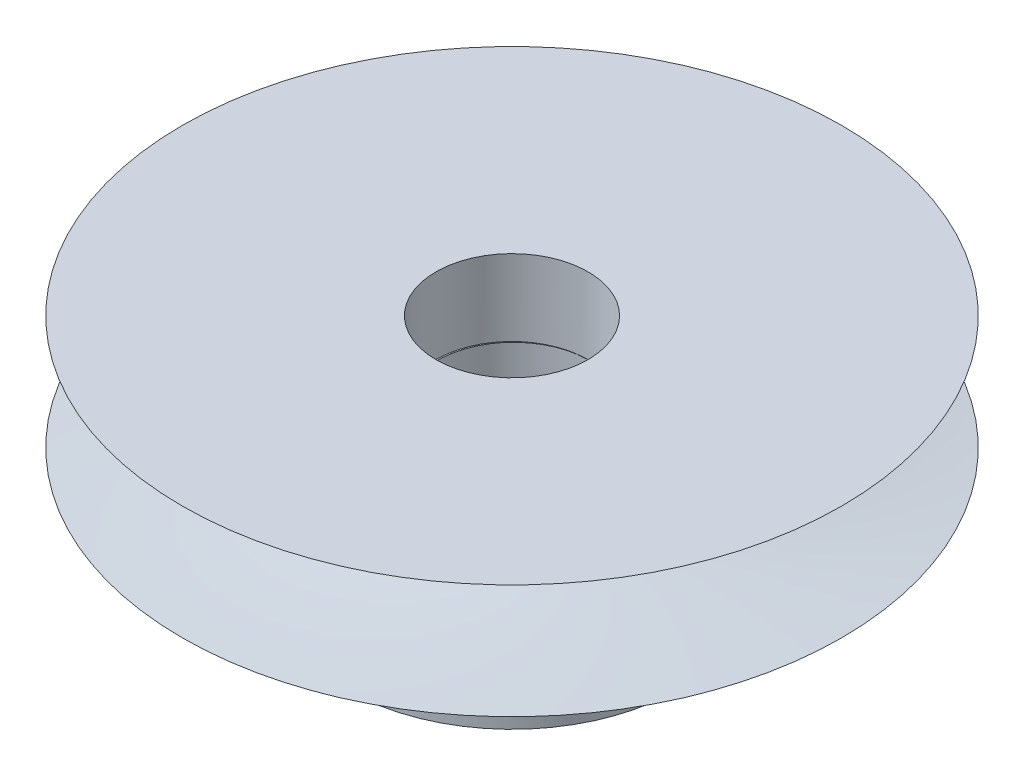
SolidWorks part; units mm, degrees
ref_plane "Front Plane" through (0, 0, 0) normal (0, 0, 1) x (1, 0, 0)
ref_plane "Top Plane" through (0, 0, 0) normal (0, 1, 0) x (1, 0, 0)
ref_plane "Right Plane" through (0, 0, 0) normal (1, 0, 0) x (0, 0, -1)
sketch "Sketch9" plane through (0, 0, 0) normal (0, 0, 1) x (1, 0, 0)
  line L0 (-4.7031, 1.5646) -> (8.2969, -1.4354) construction
  line L1 (-4.7031, -2.9354) -> (8.2969, -2.9354)
  line L3 (-4.7031, 1.5646) -> (8.2969, 1.5646)
  line L4 (8.2969, -2.9354) -> (8.2969, 1.5646)
  line L5 (8.2969, -1.4354) -> (-4.7031, -2.9354) construction
  spline S0 degree 2 poles (-4.7031, 1.5646) (8.2969, -1.4354) (-4.7031, -2.9354) knots 0 0 0 1 1 1
  dimension "D3" = 13
  dimension "D1" = 4.5
  dimension "D2" = 13
revolve "Revolve1" add sketch "Sketch9" angle 360 about L4
sketch "Sketch117" plane through (0, 1.5646, 0) normal (0, 1, 0) x (1, 0, 0)
  circle A0 centre (8.2969, 0) radius 3
extrude "Cut-Extrude4" cut sketch "Sketch117" against normal blind 3
sketch "Sketch122" plane through (0, -2.9354, 0) normal (0, -1, 0) x (-1, 0, 0)
  circle A0 centre (-8.2969, 0) radius 6.5398
extrude "Boss-Extrude1" add sketch "Sketch122" along normal blind 5
hole_wizard "M2x0.4 Tapped Hole1" positions "3DSketch1" profile "Sketch124" tap size "M2x0.4" standard "ANSI Metric" end condition through all
sketch3d "3DSketch1"
  circle A0 centre (8.2969, -2.9354, 0) radius 6.5398 construction
  circle A1 centre (8.2969, -7.9354, 0) radius 6.5398 construction
  point P0 (1.8154, -5.4316, -0.8709)
  point P5 (8.2969, -9.4751, 0)
  point P8 (8.2969, -14.4751, 0)
  dimension "D1" = 7
  dimension "D2" = 7.0027
sketch "Sketch124" plane through (1.8154, -5.4316, -0.8709) normal (0, 1, 0) x (-0.1332, 0, 0.9911)
  line L0 (0, 0) -> (0, 21.1551)
  line L1 (0, 21.1551) -> (0.8, 21.1551)
  line L2 (0.8, 21.1551) -> (0.8, 0)
  line L5 (0.8, 0) -> (0, 0)
  line L11 (0, -6.35) -> (0, 107.95) construction
  dimension "Thru Tap Drill Dia." = 1.6
  dimension "Thru Tap Drill Depth" = 21.1551
cosmetic thread "Hole Thread1" parameters "D2"=2
sketch "Sketch125" plane through (0, -1.4354, 0) normal (0, 1, 0) x (1, 0, 0)
  circle A0 centre (8.3503, 0) radius 3
extrude "Cut-Extrude5" cut sketch "Sketch125" against normal blind 7
